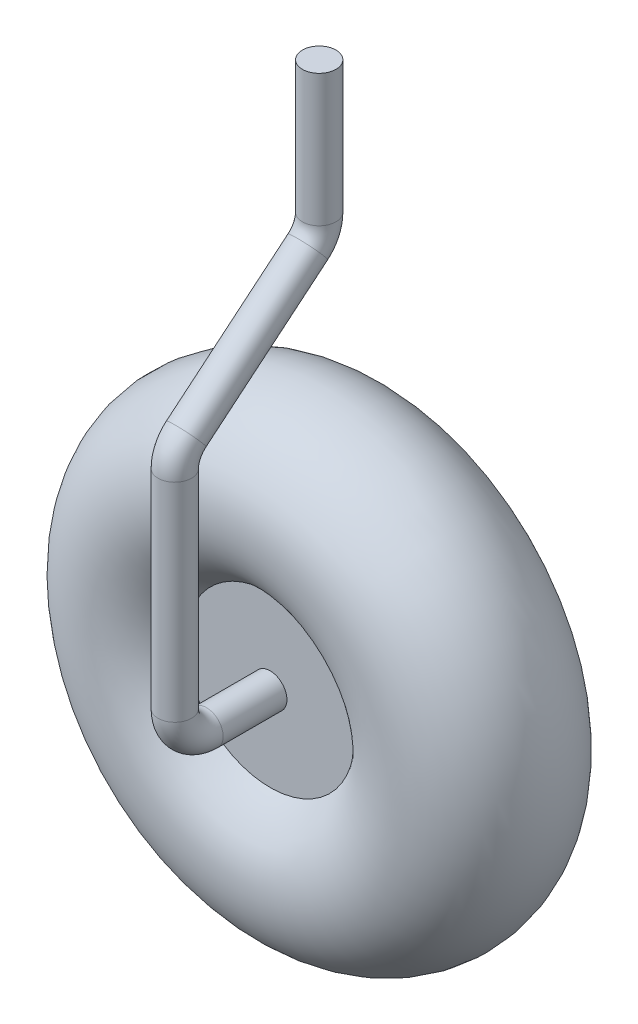
SolidWorks part; units mm, degrees
ref_plane "Front Plane" through (0, 0, 0) normal (0, 0, 1) x (1, 0, 0)
ref_plane "Top Plane" through (0, 0, 0) normal (0, 1, 0) x (1, 0, 0)
ref_plane "Right Plane" through (0, 0, 0) normal (1, 0, 0) x (0, 0, -1)
sketch "Sketch1" plane through (0, 0, 0) normal (1, 0, 0) x (0, 0, -1)
  line L0 (0, 0) -> (0, 19.05) construction
  line L1 (0, 0) -> (-12.9614, 0) construction
  line L2 (-3.9355, 0) -> (3.9355, 0)
  line L3 (-3.9355, -6.7745) -> (3.9355, -6.7745)
  line L4 (-3.9355, -6.7745) -> (-3.9355, 6.7745)
  line L5 (-3.9355, 6.7745) -> (3.9355, 6.7745)
  line L6 (3.9355, -6.7745) -> (3.9355, 6.7745)
  line L7 (-3.9355, -6.7745) -> (3.9355, 6.7745) construction
  line L8 (-3.9355, 6.7745) -> (3.9355, -6.7745) construction
  circle A0 centre (0, 12.2814) radius 6.7686
  dimension "D1" = 19.05
revolve "Revolve1" add sketch "Sketch1" angle 360 about L1
sketch "Sketch2" plane through (0, 0, 0) normal (1, 0, 0) x (0, 0, -1)
  line L0 (0, 0) -> (-9.0505, 0)
  line L1 (-11.5905, 2.54) -> (-11.5905, 19.2279)
  line L2 (-10.6758, 21.1798) -> (-0.9147, 29.3071)
  line L3 (0, 31.2591) -> (0, 41.8609)
  arc A0 (-0.9147, 29.3071) -> (0, 31.2591) centre (-2.54, 31.2591) ccw
  arc A1 (-11.5905, 19.2279) -> (-10.6758, 21.1798) centre (-9.0505, 19.2279) cw
  arc A2 (-9.0505, 0) -> (-11.5905, 2.54) centre (-9.0505, 2.54) cw
  dimension "D1" = 2.54
sketch "Sketch3" plane through (0, 0, 3.9355) normal (0, 0, 1) x (1, 0, 0)
  circle A0 centre (0, 0) radius 1.3442
sweep "Sweep1" add profiles "Sketch3" path "Sketch2"
